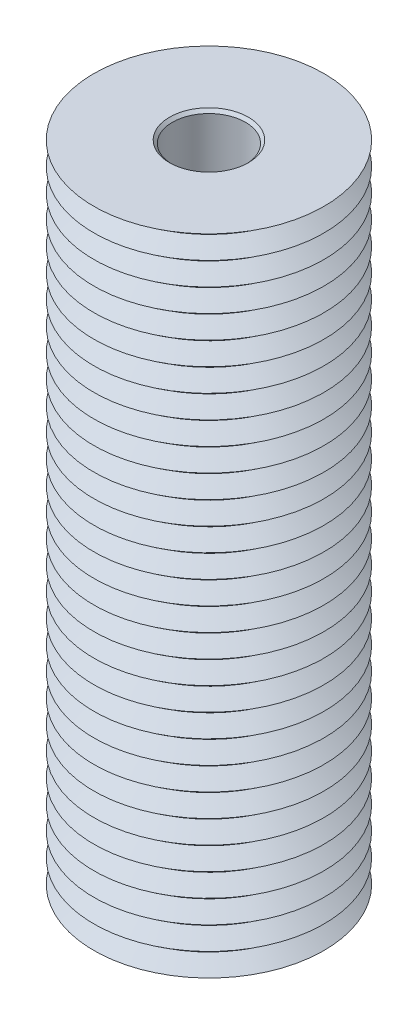
SolidWorks part; units mm, degrees
material "6061-T6 (SS)"
ref_plane "Front Plane" through (0, 0, 0) normal (0, 0, 1) x (1, 0, 0)
ref_plane "Top Plane" through (0, 0, 0) normal (0, 1, 0) x (1, 0, 0)
ref_plane "Right Plane" through (0, 0, 0) normal (1, 0, 0) x (0, 0, -1)
sketch "Sketch1" plane through (0, 0, 0) normal (0, 0, 1) x (1, 0, 0)
  line L0 (0, 0) -> (0, 29.1771) construction
  line L1 (4.3235, 28) -> (4.3235, 0) construction
  line L2 (1.7145, 0) -> (5, 0)
  line L3 (1.5875, 0.127) -> (1.5875, 27.873)
  line L4 (1.7145, 28) -> (5, 28)
  line L5 (5, 0) -> (5, 28) construction
  line L6 (5, 28) -> (4.3235, 27.5)
  line L7 (4.3235, 27.5) -> (5, 27)
  line L8 (5, 27) -> (4.3235, 26.5)
  line L9 (4.3235, 26.5) -> (5, 26)
  line L10 (5, 26) -> (4.3235, 25.5)
  line L11 (4.3235, 25.5) -> (5, 25)
  line L12 (5, 25) -> (4.3235, 24.5)
  line L13 (4.3235, 24.5) -> (5, 24)
  line L14 (5, 24) -> (4.3235, 23.5)
  line L15 (4.3235, 23.5) -> (5, 23)
  line L16 (5, 23) -> (4.3235, 22.5)
  line L17 (4.3235, 22.5) -> (5, 22)
  line L18 (5, 22) -> (4.3235, 21.5)
  line L19 (4.3235, 21.5) -> (5, 21)
  line L20 (5, 21) -> (4.3235, 20.5)
  line L21 (4.3235, 20.5) -> (5, 20)
  line L22 (5, 20) -> (4.3235, 19.5)
  line L23 (4.3235, 19.5) -> (5, 19)
  line L24 (5, 19) -> (4.3235, 18.5)
  line L25 (4.3235, 18.5) -> (5, 18)
  line L26 (5, 18) -> (4.3235, 17.5)
  line L27 (4.3235, 17.5) -> (5, 17)
  line L28 (5, 17) -> (4.3235, 16.5)
  line L29 (4.3235, 16.5) -> (5, 16)
  line L30 (5, 16) -> (4.3235, 15.5)
  line L31 (4.3235, 15.5) -> (5, 15)
  line L32 (5, 15) -> (4.3235, 14.5)
  line L33 (4.3235, 14.5) -> (5, 14)
  line L34 (5, 14) -> (4.3235, 13.5)
  line L35 (4.3235, 13.5) -> (5, 13)
  line L36 (5, 13) -> (4.3235, 12.5)
  line L37 (4.3235, 12.5) -> (5, 12)
  line L38 (5, 12) -> (4.3235, 11.5)
  line L39 (4.3235, 11.5) -> (5, 11)
  line L40 (5, 11) -> (4.3235, 10.5)
  line L41 (4.3235, 10.5) -> (5, 10)
  line L42 (5, 10) -> (4.3235, 9.5)
  line L43 (4.3235, 9.5) -> (5, 9)
  line L44 (5, 9) -> (4.3235, 8.5)
  line L45 (4.3235, 8.5) -> (5, 8)
  line L46 (5, 8) -> (4.3235, 7.5)
  line L47 (4.3235, 7.5) -> (5, 7)
  line L48 (5, 7) -> (4.3235, 6.5)
  line L49 (4.3235, 6.5) -> (5, 6)
  line L50 (5, 6) -> (4.3235, 5.5)
  line L51 (4.3235, 5.5) -> (5, 5)
  line L52 (5, 5) -> (4.3235, 4.5)
  line L53 (4.3235, 4.5) -> (5, 4)
  line L54 (5, 4) -> (4.3235, 3.5)
  line L55 (4.3235, 3.5) -> (5, 3)
  line L56 (5, 3) -> (4.3235, 2.5)
  line L57 (4.3235, 2.5) -> (5, 2)
  line L58 (5, 2) -> (4.3235, 1.5)
  line L59 (4.3235, 1.5) -> (5, 1)
  line L60 (5, 1) -> (4.3235, 0.5)
  line L61 (4.3235, 0.5) -> (5, 0)
  line L62 (1.5875, 27.873) -> (1.7145, 28)
  line L63 (1.5875, 0.127) -> (1.7145, 0)
  point P3 (1.5875, 0)
  point P5 (1.5875, 28)
  dimension "D1" = 3.175
  dimension "D2" = 4.3235
  dimension "D3" = 5
  dimension "D4" = 28
  dimension "D5" = 1
  dimension "D6" = 0.5
revolve "Revolve1" add sketch "Sketch1" angle 360 about L0
